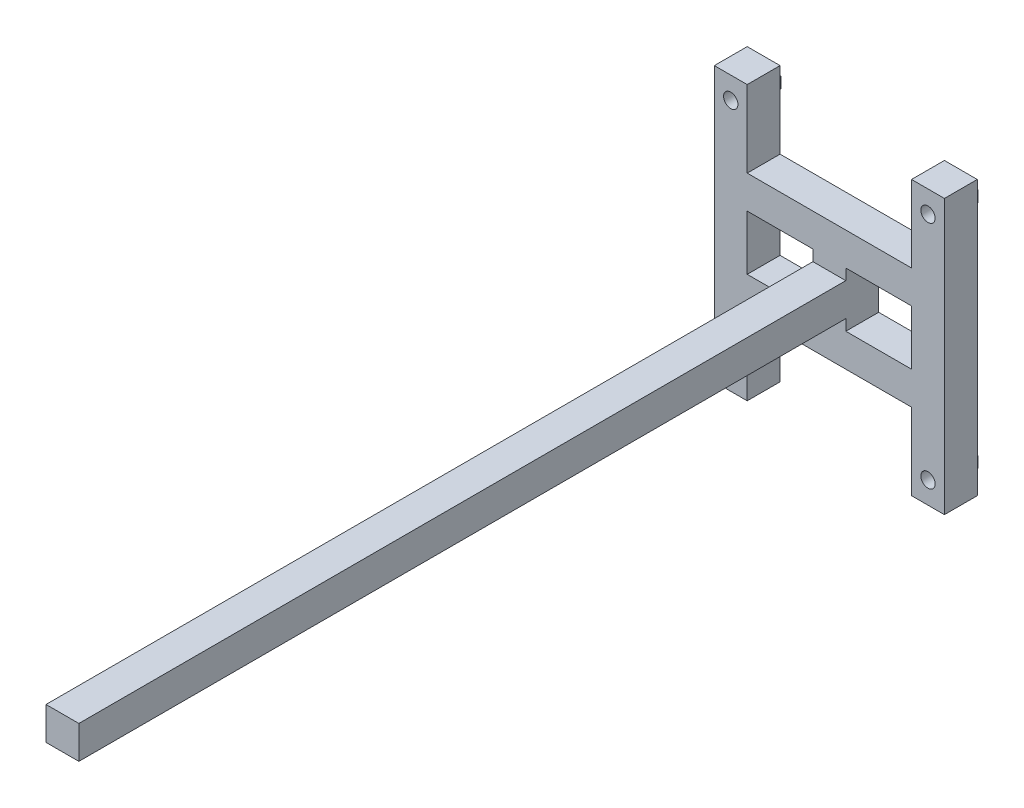
SolidWorks part; units mm, degrees
ref_plane "Front Plane" through (0, 0, 0) normal (0, 0, 1) x (1, 0, 0)
ref_plane "Top Plane" through (0, 0, 0) normal (0, 1, 0) x (1, 0, 0)
ref_plane "Right Plane" through (0, 0, 0) normal (1, 0, 0) x (0, 0, -1)
sketch "Sketch1" plane through (0, 0, 0) normal (0, 0, 1) x (1, 0, 0)
  line L0 (0, 128.3333) -> (0, 0) construction
  line L1 (-105, 125) -> (-75, 125)
  line L2 (-105, 125) -> (-105, -125)
  line L3 (-105, -125) -> (-75, -125)
  line L4 (-75, 125) -> (-75, 55)
  line L5 (0, 0) -> (133.5003, 0) construction
  line L6 (105, -125) -> (75, -125)
  line L7 (75, 125) -> (75, 55)
  line L8 (105, 125) -> (75, 125)
  line L9 (105, 125) -> (105, -125)
  line L10 (-75, -25) -> (-15, -25)
  line L11 (-75, 55) -> (75, 55)
  line L13 (-75, 25) -> (-15, 25)
  line L16 (-75, -55) -> (75, -55)
  line L18 (-75, 25) -> (-75, -25)
  line L19 (-75, -55) -> (-75, -125)
  line L20 (75, -55) -> (75, -125)
  line L21 (75, 25) -> (75, -25)
  line L22 (15, 25) -> (75, 25)
  line L24 (15, -25) -> (15, 25)
  line L26 (-15, -25) -> (-15, 25)
  line L27 (15, -25) -> (-15, 25) construction
  line L28 (15, 25) -> (-15, -25) construction
  line L29 (15, -25) -> (75, -25)
  dimension "D1" = 30
  dimension "D2" = 250
  dimension "D3" = 30
  dimension "D4" = 50
  dimension "D5" = 150
  dimension "D6" = 30
extrude "Boss-Extrude1" add sketch "Sketch1" along normal blind 30
sketch "Sketch2" plane through (0, 0, 30) normal (0, 0, 1) x (1, 0, 0)
  line L0 (-15, -25) -> (-15, 25) construction
  line L1 (15, -15) -> (-15, -15)
  line L2 (15, -15) -> (15, 15)
  line L3 (15, 15) -> (-15, 15)
  line L4 (-15, -15) -> (-15, 15)
  line L5 (15, -15) -> (-15, 15) construction
  line L6 (15, 15) -> (-15, -15) construction
  point P0 (0, 0)
  dimension "D1" = 30
extrude "Boss-Extrude2" add sketch "Sketch2" along normal blind 700
sketch "Sketch3" plane through (0, 0, 0) normal (0, 0, -1) x (-1, 0, 0)
  line L0 (0, 55) -> (0, 0) construction
  line L1 (-75, 55) -> (75, 55) construction
  line L2 (0, 0) -> (105, 0) construction
  line L3 (105, 125) -> (105, -125) construction
  line L4 (-90, 125) -> (-90, -125) construction
  line L5 (-105, 125) -> (-75, 125) construction
  line L6 (-75, -125) -> (-105, -125) construction
  line L7 (81.3397, 110) -> (90, 115)
  line L8 (-90, 115) -> (-98.6603, 110)
  line L9 (-98.6603, 110) -> (-98.6603, 100)
  line L10 (-98.6603, 100) -> (-90, 95)
  line L11 (-90, 95) -> (-81.3397, 100)
  line L12 (-81.3397, 100) -> (-81.3397, 110)
  line L13 (-81.3397, 110) -> (-90, 115)
  line L14 (81.3397, 100) -> (81.3397, 110)
  line L15 (90, 95) -> (81.3397, 100)
  line L16 (98.6603, 100) -> (90, 95)
  line L17 (98.6603, 110) -> (98.6603, 100)
  line L18 (90, 115) -> (98.6603, 110)
  line L19 (81.3397, -100) -> (81.3397, -110)
  line L20 (90, -95) -> (81.3397, -100)
  line L21 (98.6603, -100) -> (90, -95)
  line L22 (98.6603, -110) -> (98.6603, -100)
  line L23 (90, -115) -> (98.6603, -110)
  line L24 (81.3397, -110) -> (90, -115)
  line L25 (-81.3397, -110) -> (-90, -115)
  line L26 (-81.3397, -100) -> (-81.3397, -110)
  line L27 (-90, -95) -> (-81.3397, -100)
  line L28 (-98.6603, -100) -> (-90, -95)
  line L29 (-98.6603, -110) -> (-98.6603, -100)
  line L30 (-90, -115) -> (-98.6603, -110)
  circle A0 centre (-90, 105) radius 6
  circle A1 centre (-90, 105) radius 8.6603 construction
  circle A2 centre (90, 105) radius 6
  circle A3 centre (90, -105) radius 6
  circle A4 centre (-90, -105) radius 6
  dimension "D1" = 12
  dimension "D2" = 10
  dimension "D3" = 20
extrude "Boss-Extrude3" add sketch "Sketch3" along normal blind 7
sketch "Sketch4" plane through (0, 0, 0) normal (0, 0, -1) x (-1, 0, 0)
  line L0 (0, 55) -> (0, 0) construction
  line L1 (-75, 55) -> (75, 55) construction
  line L2 (0, 0) -> (105, 0) construction
  line L3 (105, 125) -> (105, -125) construction
  circle A0 centre (-90, 105) radius 6.5238
  circle A1 centre (90, 105) radius 6.5238
  circle A2 centre (90, -105) radius 6.5238
  circle A3 centre (-90, -105) radius 6.5238
extrude "Cut-Extrude1" cut sketch "Sketch4" against normal up to next
